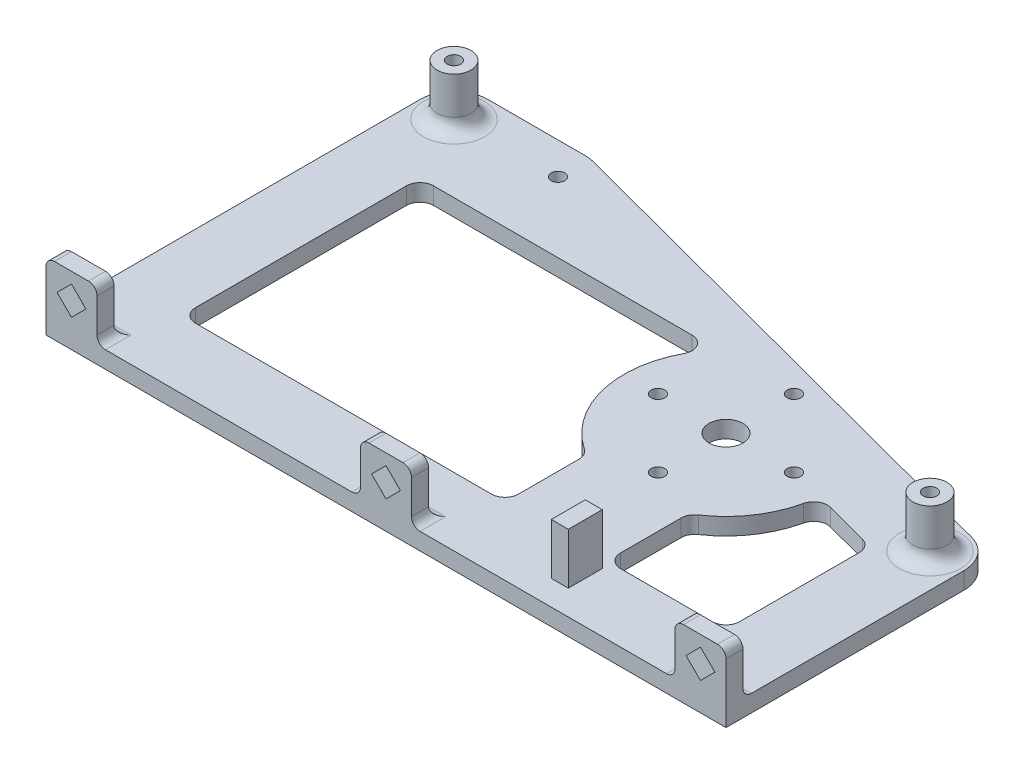
SolidWorks part; units mm, degrees
ref_plane "Front Plane" through (0, 0, 0) normal (0, 0, 1) x (1, 0, 0)
ref_plane "Top Plane" through (0, 0, 0) normal (0, 1, 0) x (1, 0, 0)
ref_plane "Right Plane" through (0, 0, 0) normal (1, 0, 0) x (0, 0, -1)
sketch "Sketch1" plane through (0, 0, 0) normal (0, 1, 0) x (1, 0, 0)
  line L0 (-57.15, 25.7742) -> (169.7943, 86.5838) construction
  line L1 (-48.962, 19.7507) -> (-53.0707, 35.0848) construction
  line L2 (-48.962, 19.7507) -> (171.8486, 78.9167) construction
  line L3 (-53.0707, 35.0848) -> (167.7399, 94.2508) construction
  line L4 (171.8486, 78.9167) -> (167.7399, 94.2508) construction
  line L5 (0, 0) -> (38.1, 0) construction
  line L6 (-82.55, 31.75) -> (-82.55, -44.45)
  line L7 (-82.55, -44.45) -> (44.45, -44.45)
  line L8 (44.45, -44.45) -> (44.45, 4.8894)
  line L9 (44.45, 4.8894) -> (-57.15, 31.75)
  line L10 (-57.15, 31.75) -> (-82.55, 31.75)
  circle A0 centre (0, 0) radius 3.175
  circle A1 centre (0, 12.7) radius 1.27
  circle A2 centre (12.7, 0) radius 1.27
  circle A3 centre (0, -12.7) radius 1.27
  circle A4 centre (-12.7, 0) radius 1.27
  circle A5 centre (0, 0) radius 12.7 construction
  circle A6 centre (-57.15, 25.7742) radius 1.27
  circle A7 centre (0, 0) radius 31.75 construction
  circle A8 centre (-76.2, 25.4) radius 1.27
  circle A9 centre (38.1, 0) radius 1.27
  dimension "D1" = 6.35
  dimension "D2" = 2.54
  dimension "D3" = 25.4
  dimension "D5" = 63.5
  dimension "D10" = 2.54
  dimension "D11" = 2.54
  dimension "D14" = 2.54
  dimension "D4" = 57.15
  dimension "D6" = 15.875
  dimension "D7" = 15
  dimension "D8" = 228.6
  dimension "D9" = 6.35
  dimension "D12" = 25.4
  dimension "D13" = 76.2
  dimension "D15" = 38.1
  dimension "D16" = 6.35
  dimension "D17" = 6.35
  dimension "D18" = 6.35
  dimension "D19" = 6.35
  dimension "D20" = 25.4
  dimension "D21" = 76.2
extrude "Boss-Extrude1" add sketch "Sketch1" along normal blind 3.175
sketch "Sketch2" plane through (0, 3.175, 0) normal (0, 1, 0) x (1, 0, 0)
  line L0 (-69.85, 10.16) -> (-69.85, -29.21)
  line L1 (-67.31, -31.75) -> (-12.065, -31.75)
  line L2 (-9.525, -29.21) -> (-9.525, -17.9043)
  line L3 (-82.55, 31.75) -> (-82.55, -44.45) construction
  line L4 (-19.05, 12.7) -> (-67.31, 12.7)
  line L5 (-57.15, 31.75) -> (-82.55, 31.75) construction
  line L6 (-82.55, -44.45) -> (44.45, -44.45) construction
  line L7 (9.525, -17.9043) -> (9.525, -29.21)
  line L8 (12.065, -31.75) -> (29.21, -31.75)
  line L9 (31.75, -29.21) -> (31.75, -6.8451)
  line L10 (29.8592, -4.3895) -> (21.7227, -2.2384)
  line L11 (44.45, -44.45) -> (44.45, 4.8894) construction
  line L12 (44.45, 4.8894) -> (-57.15, 31.75) construction
  arc A0 (-10.6456, -15.7979) -> (-16.8088, 8.9647) centre (0, 0) cw
  arc A1 (10.6456, -15.7979) -> (18.5943, -4.1418) centre (0, 0) ccw
  arc A2 (29.8592, -4.3895) -> (31.75, -6.8451) centre (29.21, -6.8451) cw
  arc A3 (29.21, -31.75) -> (31.75, -29.21) centre (29.21, -29.21) ccw
  arc A4 (12.065, -31.75) -> (9.525, -29.21) centre (12.065, -29.21) cw
  arc A5 (9.525, -17.9043) -> (10.6456, -15.7979) centre (12.065, -17.9043) cw
  arc A6 (18.5943, -4.1418) -> (21.7227, -2.2384) centre (21.0735, -4.694) cw
  arc A7 (-19.05, 12.7) -> (-16.8088, 8.9647) centre (-19.05, 10.16) cw
  arc A8 (-9.525, -17.9043) -> (-10.6456, -15.7979) centre (-12.065, -17.9043) ccw
  arc A9 (-12.065, -31.75) -> (-9.525, -29.21) centre (-12.065, -29.21) ccw
  arc A10 (-67.31, -31.75) -> (-69.85, -29.21) centre (-67.31, -29.21) cw
  arc A11 (-69.85, 10.16) -> (-67.31, 12.7) centre (-67.31, 10.16) cw
  dimension "D1" = 19.05
  dimension "D9" = 2.54
  dimension "D2" = 12.7
  dimension "D3" = 19.05
  dimension "D4" = 12.7
  dimension "D5" = 9.525
  dimension "D6" = 9.525
  dimension "D7" = 12.7
  dimension "D8" = 12.7
extrude "Cut-Extrude1" cut sketch "Sketch2" against normal blind 3.175
fillet "Fillet1" radius 6.35 3 edges at (44.45, 1.5875, -4.8894) (-82.55, 1.5875, -31.75) (-57.15, 1.5875, -31.75)
sketch "Sketch3" plane through (0, 0, 44.45) normal (0, 0, 1) x (1, 0, 0)
  line L0 (-82.55, 3.175) -> (-73.025, 3.175)
  line L1 (-82.55, 3.175) -> (-82.55, 12.7)
  line L2 (-73.025, 3.175) -> (-73.025, 12.7)
  line L3 (-82.55, 12.7) -> (-73.025, 12.7)
  line L4 (-82.55, 3.175) -> (44.45, 3.175) construction
  line L5 (-77.7875, 5.2434) -> (-75.0934, 7.9375)
  line L6 (44.45, 3.175) -> (34.925, 3.175)
  line L7 (44.45, 3.175) -> (44.45, 12.7)
  line L8 (44.45, 12.7) -> (34.925, 12.7)
  line L9 (34.925, 3.175) -> (34.925, 12.7)
  line L10 (-23.8125, 3.175) -> (-14.2875, 3.175)
  line L11 (-23.8125, 3.175) -> (-23.8125, 12.7)
  line L12 (-23.8125, 12.7) -> (-14.2875, 12.7)
  line L13 (-14.2875, 3.175) -> (-14.2875, 12.7)
  line L14 (-77.7875, 5.2434) -> (-80.4816, 7.9375)
  line L15 (-75.0934, 7.9375) -> (-77.7875, 10.6316)
  line L16 (-80.4816, 7.9375) -> (-77.7875, 10.6316)
  line L17 (-77.7875, 5.2434) -> (-77.7875, 10.6316) construction
  line L18 (-75.0934, 7.9375) -> (-80.4816, 7.9375) construction
  line L19 (-19.05, 5.2434) -> (-16.3559, 7.9375)
  line L20 (-19.05, 5.2434) -> (-21.7441, 7.9375)
  line L21 (-16.3559, 7.9375) -> (-19.05, 10.6316)
  line L22 (-21.7441, 7.9375) -> (-19.05, 10.6316)
  line L23 (-19.05, 5.2434) -> (-19.05, 10.6316) construction
  line L24 (-16.3559, 7.9375) -> (-21.7441, 7.9375) construction
  line L25 (39.6875, 5.2434) -> (42.3816, 7.9375)
  line L26 (39.6875, 5.2434) -> (36.9934, 7.9375)
  line L27 (42.3816, 7.9375) -> (39.6875, 10.6316)
  line L28 (36.9934, 7.9375) -> (39.6875, 10.6316)
  line L29 (39.6875, 5.2434) -> (39.6875, 10.6316) construction
  line L30 (42.3816, 7.9375) -> (36.9934, 7.9375) construction
  point P17 (-77.7875, 7.9375)
  point P18 (-19.05, 7.9375)
  point P19 (-77.7875, 7.9375)
  point P20 (-19.05, 7.9375)
  point P29 (39.6875, 7.9375)
  point P30 (39.6875, 7.9375)
  dimension "D1" = 9.525
  dimension "D2" = 9.525
  dimension "D3" = 4.7625
  dimension "D4" = 4.7625
  dimension "D5" = 3.81
  dimension "D6" = 3.81
  dimension "D7" = 4.7625
  dimension "D8" = 4.7625
  dimension "D9" = 3.81
  dimension "D10" = 4.7625
  dimension "D11" = 4.7625
  dimension "D12" = 49.2125
  dimension "D13" = 127
extrude "Boss-Extrude2" add sketch "Sketch3" against normal blind 3.175
fillet "Fillet2" radius 1.5875 13 edges at (-23.8125, 12.7, 42.8625) (-14.2875, 12.7, 42.8625) (34.925, 12.7, 42.8625) (44.45, 12.7, 42.8625) (34.925, 3.175, 42.8625) (39.6875, 3.175, 41.275) (-14.2875, 3.175, 42.8625) (-23.8125, 3.175, 42.8625) (-19.05, 3.175, 41.275) (-82.55, 12.7, 42.8625) (-73.025, 12.7, 42.8625) (-73.025, 3.175, 42.8625) (-77.7875, 3.175, 41.275)
sketch "Sketch4" plane through (0, 3.175, 0) normal (0, 1, 0) x (1, 0, 0)
  circle A0 centre (-76.2, 25.4) radius 3.175
  circle A1 centre (38.1, 0) radius 3.175
  circle A2 centre (38.1, 0) radius 1.27 construction
  circle A3 centre (38.1, 0) radius 1.27
  circle A4 centre (-76.2, 25.4) radius 1.27 construction
  circle A5 centre (-76.2, 25.4) radius 1.27
  dimension "D1" = 6.35
  dimension "D2" = 6.35
extrude "Boss-Extrude3" add sketch "Sketch4" along normal blind 9.525
sketch "Sketch5" plane through (0, 3.175, 0) normal (0, 1, 0) x (1, 0, 0)
  line L0 (0, 0) -> (8.7515, -30.5201)
  line L1 (9.525, -17.9043) -> (9.525, -29.21) construction
  line L3 (5.767, -30.5201) -> (11.736, -30.5201)
  line L4 (5.767, -30.5201) -> (5.767, -33.4411)
  line L5 (5.767, -33.4411) -> (11.736, -33.4411)
  line L6 (11.736, -30.5201) -> (11.736, -33.4411)
  line L7 (7.164, -33.4411) -> (10.339, -33.4411)
  line L8 (7.164, -33.4411) -> (7.164, -39.7911)
  line L9 (7.164, -39.7911) -> (10.339, -39.7911)
  line L10 (10.339, -33.4411) -> (10.339, -39.7911)
  circle A0 centre (0, 0) radius 31.75
  point P10 (8.7515, -30.5201)
  point P15 (8.7515, -33.4411)
  dimension "D1" = 63.5
  dimension "D2" = 16
  dimension "D3" = 5.969
  dimension "D4" = 2.921
  dimension "D5" = 6.35
  dimension "D6" = 3.175
extrude "Boss-Extrude4" add sketch "Sketch5" along normal blind 9.525 contours L10 L5 L8 L9
fillet "Fillet4" radius 2.54 2 edges at (38.1, 3.175, 3.175) (-76.2, 3.175, -22.225)
equation "\"D1@Sketch4\"=\"D2@Sketch4\""
